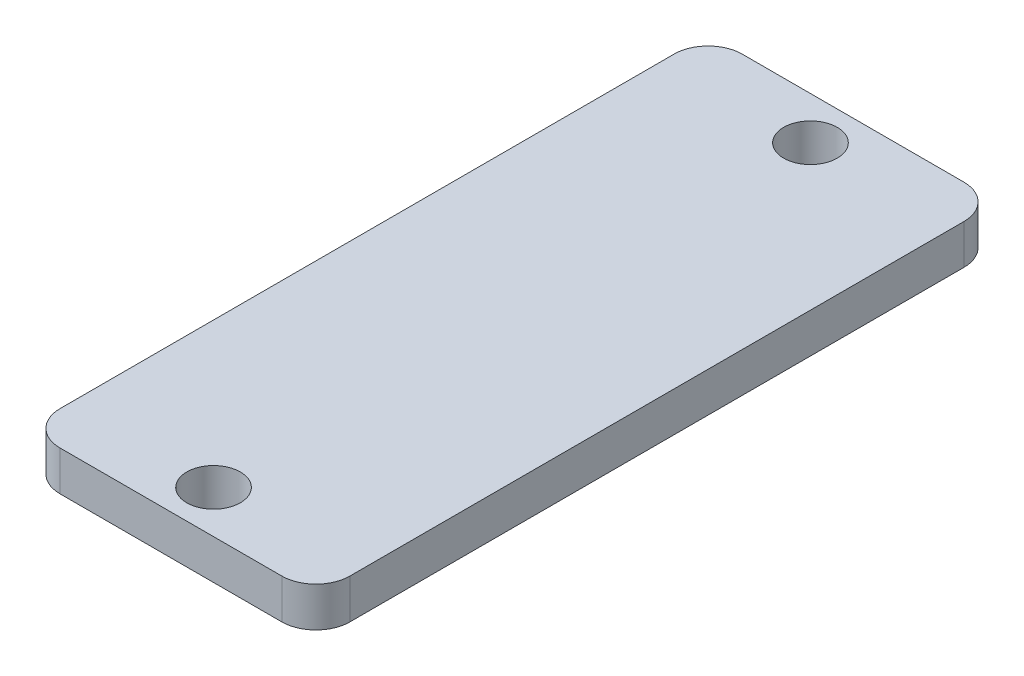
SolidWorks part; units mm, degrees
ref_plane "Front Plane" through (0, 0, 0) normal (0, 0, 1) x (1, 0, 0)
ref_plane "Top Plane" through (0, 0, 0) normal (0, 1, 0) x (1, 0, 0)
ref_plane "Right Plane" through (0, 0, 0) normal (1, 0, 0) x (0, 0, -1)
sketch "Sketch1" plane through (0, 0, 0) normal (0, 1, 0) x (1, 0, 0)
  line L0 (0, -22.225) -> (0, 22.225) construction
  line L1 (-10.795, 19.05) -> (10.795, 19.05) construction
  line L2 (-10.795, 19.05) -> (-10.795, -19.05) construction
  line L3 (-10.795, -19.05) -> (10.795, -19.05) construction
  line L4 (10.795, 19.05) -> (10.795, -19.05) construction
  line L5 (-10.795, 19.05) -> (10.795, -19.05) construction
  line L6 (-10.795, -19.05) -> (10.795, 19.05) construction
  line L7 (-10.795, -25.4) -> (10.795, -25.4)
  line L8 (-10.795, -25.4) -> (-10.795, 25.4)
  line L9 (-10.795, 25.4) -> (10.795, 25.4)
  line L10 (10.795, -25.4) -> (10.795, 25.4)
  line L11 (-10.795, -25.4) -> (10.795, 25.4) construction
  line L12 (-10.795, 25.4) -> (10.795, -25.4) construction
  circle A0 centre (0, 22.225) radius 1.9939
  circle A1 centre (0, -22.225) radius 1.9939
  point P0 (0, 0)
  point P10 (0, 0)
  point P15 (0, 0)
  dimension "D3" = 3.9878
  dimension "D4" = 44.45
  dimension "D6" = 3.175
  dimension "D1" = 21.59
  dimension "D2" = 38.1
extrude "Boss-Extrude1" add sketch "Sketch1" along normal blind 2.9591
fillet "Fillet1" radius 2.54 4 edges at (10.795, 1.4796, -25.4) (-10.795, 1.4796, -25.4) (-10.795, 1.4796, 25.4) (10.795, 1.4796, 25.4)
